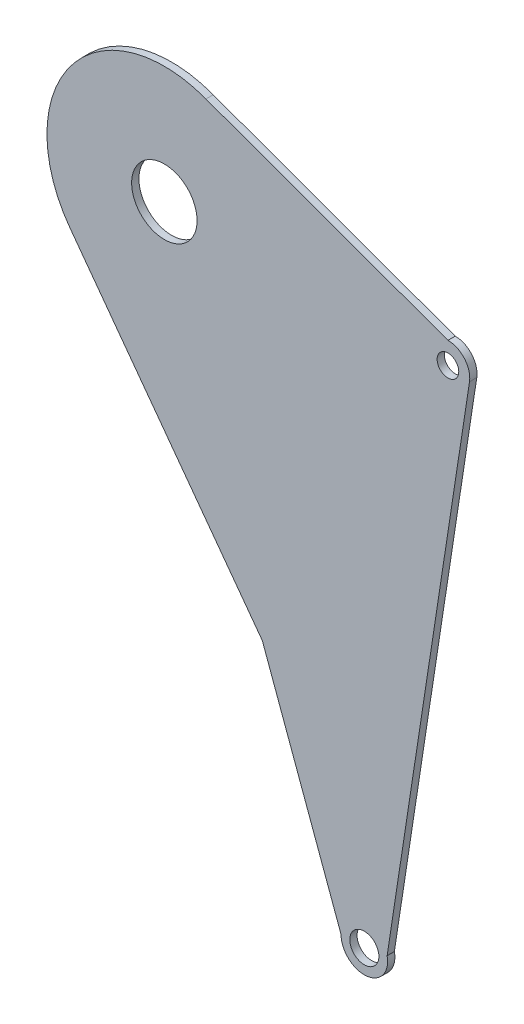
SolidWorks part; units mm, degrees
ref_plane "Front Plane" through (0, 0, 0) normal (0, 0, 1) x (1, 0, 0)
ref_plane "Top Plane" through (0, 0, 0) normal (0, 1, 0) x (1, 0, 0)
ref_plane "Right Plane" through (0, 0, 0) normal (1, 0, 0) x (0, 0, -1)
sketch "Sketch1" plane through (0, 0, 0) normal (0, 0, 1) x (1, 0, 0)
  line L0 (0, 0) -> (123.825, 0)
  line L1 (123.825, 0) -> (87.3125, -238.5215)
  line L2 (87.3125, -238.5215) -> (0, 0)
  line L3 (0, 0) -> (123.825, 0) construction
  line L4 (0, 9.525) -> (123.825, 9.525)
  line L5 (0, -9.525) -> (123.825, -9.525)
  line L6 (0, 0) -> (87.3125, -238.5215) construction
  line L7 (8.9446, 3.2742) -> (96.2571, -235.2473)
  line L8 (-8.9446, -3.2742) -> (78.3679, -241.7958)
  line L9 (87.3125, -238.5215) -> (123.825, 0) construction
  line L10 (77.8972, -237.0803) -> (114.4097, 1.4413)
  line L11 (96.7278, -239.9628) -> (133.2403, -1.4413)
  line L12 (34.7117, -122.535) -> (-39.5279, -32.6463)
  line L13 (123.825, 9.525) -> (17.5192, 48.18)
  arc A0 (0, 9.525) -> (0, -9.525) centre (0, 0) ccw
  arc A1 (123.825, -9.525) -> (123.825, 9.525) centre (123.825, 0) ccw
  arc A2 (8.9446, 3.2742) -> (-8.9446, -3.2742) centre (0, 0) ccw
  arc A3 (78.3679, -241.7958) -> (96.2571, -235.2473) centre (87.3125, -238.5215) ccw
  arc A4 (77.8972, -237.0803) -> (96.7278, -239.9628) centre (87.3125, -238.5215) ccw
  arc A5 (133.2403, -1.4413) -> (114.4097, 1.4413) centre (123.825, 0) ccw
  circle A6 centre (0, 0) radius 14.2875
  circle A7 centre (123.825, 0) radius 4.7244
  circle A8 centre (87.3125, -238.5215) radius 6.35
  circle A9 centre (0, 0) radius 51.2663
  circle A10 centre (0, 0) radius 26.9875
  point P3 (61.9125, 0)
  point P10 (43.6563, -119.2608)
  point P15 (105.5688, -119.2608)
  dimension "D4" = 28.575
  dimension "D5" = 9.4488
  dimension "D6" = 12.7
  dimension "D7" = 9.525
  dimension "D8" = 12.7
  dimension "D1" = 123.825
  dimension "D2" = 241.3
  dimension "D3" = 254
extrude "Boss-Extrude1" add sketch "Sketch1" along normal blind 3.175 contours A10 L5 L10 L0 | A10 L0 L10 A5 L4 | A10 L2 L10 L7 | A10 L8 A4 L10 L2 | A3 L11 A1 L5 L1 L7 | L10 L7 L1 L5 | A7 L0 L10 L5 L1 | A7 L1 L5 A1 A5 L10 L0 | A8 L1 L7 L10 L2 | A8 L2 L10 A4 A3 L7 L1 | A10 L7 L10 L5 | L4 A6 L8 A0 | L7 A2 A0 L5 L2 L0 | L5 A6 L7 L0 L2 | L7 A6 L0 | L0 A6 L4 A2 L7 | L8 A6 L2 L5 A0 | L2 A6 L5 | A9
sketch "Sketch2" plane through (0, 0, 0) normal (0, 0, -1) x (-1, 0, 0)
  circle A0 centre (-87.3125, -238.5215) radius 10.16
  circle A1 centre (-87.3125, -238.5215) radius 9.525
  dimension "D1" = 20.32
extrude "Boss-Extrude2" add sketch "Sketch2" against normal up to surface (3.175 mm away) up to face at (70.4569, -78.2987, 3.175)
sketch "Sketch3" plane through (0, 0, 0) normal (0, 0, -1) x (-1, 0, 0)
  line L0 (-42.762, -144.5269) -> (41.2454, -30.4475)
  line L1 (-8.3714, -50.5782) -> (-77.1526, -238.4757) construction
  line L2 (-123.825, 9.525) -> (-16.8758, 48.4091)
  line L3 (-8.3714, -50.5782) -> (-42.762, -144.5269)
  line L4 (-50.3737, 9.525) -> (-123.825, 9.525)
  arc A0 (-8.3714, -50.5782) -> (-50.3737, 9.525) centre (0, 0) ccw construction
  arc A1 (-16.8758, 48.4091) -> (-50.3737, 9.525) centre (0, 0) ccw
  arc A2 (41.2454, -30.4475) -> (-8.3714, -50.5782) centre (0, 0) cw
  line M6 (-77.1526, -238.4757) -> (-8.3714, -50.5782)
  arc M7 (-8.3714, -50.5782) -> (-50.3737, 9.525) centre (0, 0) ccw
  line M8 (-50.3737, 9.525) -> (-123.825, 9.525)
extrude "Boss-Extrude3" add sketch "Sketch3" against normal up to surface (3.175 mm away) contours L2 M8 M7 | L0 M6 M7 up to face at (70.4108, -77.8361, 3.175)
